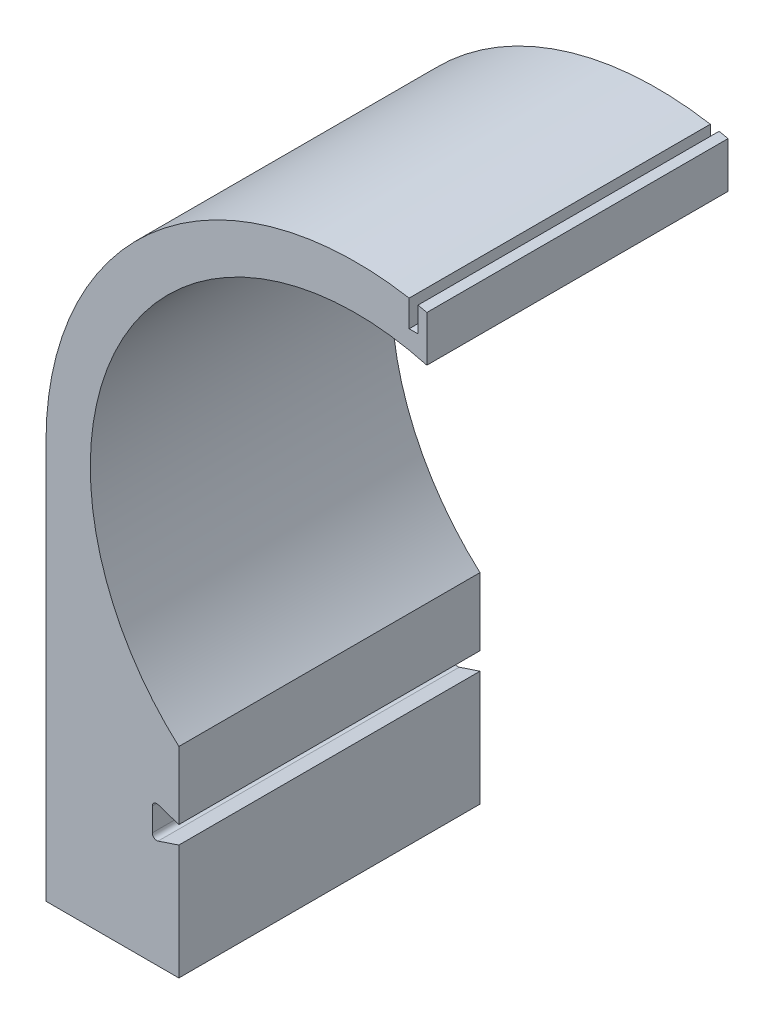
SolidWorks part; units mm, degrees
material "201 Annealed Stainless Steel (SS)"
ref_plane "Front Plane" through (0, 0, 0) normal (0, 0, 1) x (1, 0, 0)
ref_plane "Top Plane" through (0, 0, 0) normal (0, 1, 0) x (1, 0, 0)
ref_plane "Right Plane" through (0, 0, 0) normal (1, 0, 0) x (0, 0, -1)
sketch "Sketch1" plane through (0, 0, 0) normal (0, 0, 1) x (1, 0, 0)
  line L0 (0, 0) -> (0, -175) construction
  line L1 (-100, -111.8034) -> (-100, -150)
  line L2 (0, 0) -> (101.5936, 0) construction
  line L3 (40, 113.7839) -> (40, -22.985) construction
  line L5 (40, 170.3673) -> (40, 144.5683)
  line L7 (0, 0) -> (-138.7196, 0) construction
  line L8 (-175, 0) -> (-175, -225)
  line L9 (-100, -225) -> (-175, -225)
  line L10 (0, -175) -> (0, -225) construction
  line L11 (0, -225) -> (-200, -225) construction
  line L12 (-100, -111.8034) -> (100, -111.8034) construction
  line L13 (0, -150) -> (-100, -150) construction
  line L14 (35, 171.4643) -> (35, 157.4094)
  line L15 (35, 157.4094) -> (30, 157.4094)
  line L16 (30, 157.4094) -> (30, 172.4094)
  line L18 (-100, -160) -> (-111.7094, -163.9031)
  line L19 (-115, -161.5314) -> (-115, -148.4686)
  line L20 (-111.7094, -146.0969) -> (-100, -150)
  line L21 (-100, -150) -> (-100, -160) construction
  line L22 (-100, -160) -> (-100, -225)
  line L23 (-100, -150) -> (-100, -160) construction
  line L24 (-100, -155) -> (-115, -155) construction
  circle A0 centre (0, 0) radius 150 construction
  circle A1 centre (0, 0) radius 175 construction
  arc A2 (-100, -111.8034) -> (40, 144.5683) centre (0, 0) cw
  arc A3 (-175, 0) -> (30, 172.4094) centre (0, 0) cw
  arc A4 (35, 171.4643) -> (40, 170.3673) centre (0, 0) cw
  arc A5 (-115, -148.4686) -> (-111.7094, -146.0969) centre (-112.5, -148.4686) cw
  arc A6 (-115, -161.5314) -> (-111.7094, -163.9031) centre (-112.5, -161.5314) ccw
  point P31 (-115, -145)
  point P34 (-115, -165)
  dimension "D1" = 300
  dimension "D2" = 350
  dimension "D6" = 175
  dimension "D5" = 50
  dimension "D13" = 2.5
  dimension "D14" = 2.5
  dimension "D3" = 5
  dimension "D4" = 30
  dimension "D7" = 200
  dimension "D8" = 5
  dimension "D9" = 15
  dimension "D10" = 20
  dimension "D11" = 15
  dimension "D12" = 10
extrude "Inner Ring - Left Side" add sketch "Sketch1" along normal blind 170
sketch "Sketch2" plane through (-100, 0, 0) normal (1, 0, 0) x (0, 0, -1)
  line L0 (0, -150) -> (-170, -150) construction
  line L1 (-170, -150) -> (-170, -111.8034) construction
